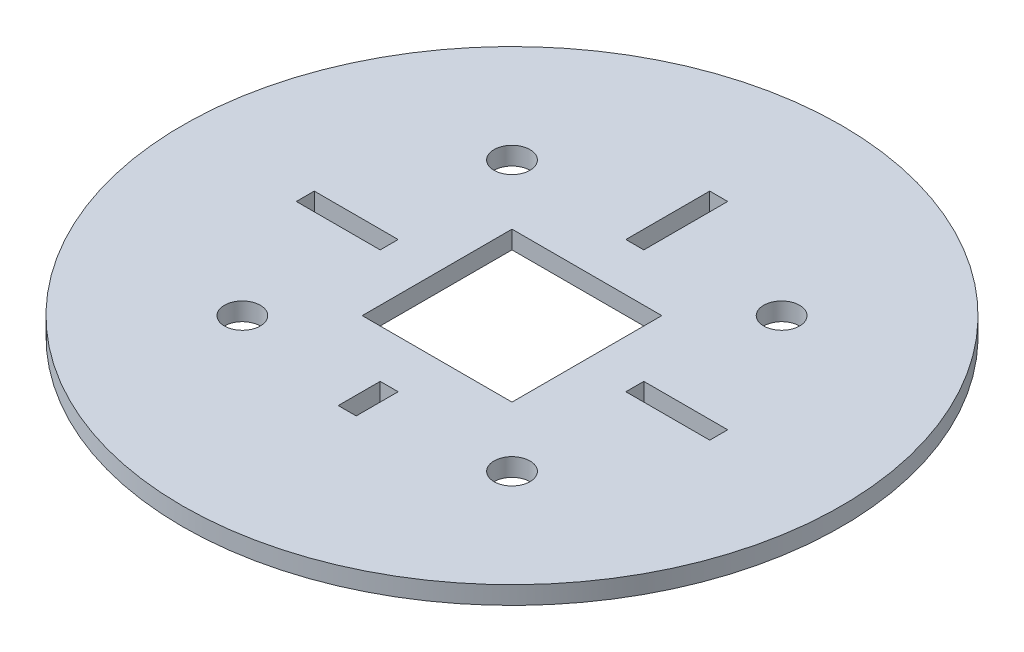
SolidWorks part; units mm, degrees
ref_plane "Front Plane" through (0, 0, 0) normal (0, 0, 1) x (1, 0, 0)
ref_plane "Top Plane" through (0, 0, 0) normal (0, 1, 0) x (1, 0, 0)
ref_plane "Right Plane" through (0, 0, 0) normal (1, 0, 0) x (0, 0, -1)
sketch "Sketch1" plane through (0, 0, 0) normal (0, 1, 0) x (1, 0, 0)
  circle A0 centre (0, 0) radius 55
  dimension "D1" = 110
extrude "Boss-Extrude1" add sketch "Sketch1" along normal blind 3 contours A0
sketch "Sketch2" plane through (0, 3, 0) normal (0, 1, 0) x (1, 0, 0)
  line L0 (0, 0) -> (0, 27.5) construction
  line L1 (12.5, 12.5) -> (-12.5, 12.5)
  line L2 (12.5, 12.5) -> (12.5, -12.5)
  line L3 (12.5, -12.5) -> (-12.5, -12.5)
  line L4 (-12.5, 12.5) -> (-12.5, -12.5)
  line L5 (12.5, 12.5) -> (-12.5, -12.5) construction
  line L6 (12.5, -12.5) -> (-12.5, 12.5) construction
  line L8 (1.5, 34.5) -> (-1.5, 20.5) construction
  line L9 (-1.5, 34.5) -> (1.5, 20.5) construction
  line L10 (-1.5, 20.5) -> (1.5, 20.5)
  line L11 (1.5, 34.5) -> (1.5, 20.5)
  line L12 (-1.5, 34.5) -> (1.5, 34.5)
  line L13 (-34.5, 1.5) -> (-20.5, 1.5)
  line L14 (-34.5, 1.5) -> (-34.5, -1.5)
  line L15 (-34.5, -1.5) -> (-20.5, -1.5)
  line L16 (-20.5, 1.5) -> (-20.5, -1.5)
  line L17 (-34.5, 1.5) -> (-20.5, -1.5) construction
  line L18 (-34.5, -1.5) -> (-20.5, 1.5) construction
  line L19 (-1.5, 34.5) -> (-1.5, 20.5)
  line L20 (20.5, 1.5) -> (34.5, 1.5)
  line L21 (-1.5, -20.5) -> (1.5, -20.5)
  line L22 (-1.5, -20.5) -> (-1.5, -27.5)
  line L23 (-1.5, -27.5) -> (1.5, -27.5)
  line L24 (1.5, -20.5) -> (1.5, -27.5)
  line L25 (-1.5, -20.5) -> (1.5, -27.5) construction
  line L26 (20.5, 1.5) -> (20.5, -1.5)
  line L27 (20.5, -1.5) -> (34.5, -1.5)
  line L28 (34.5, 1.5) -> (34.5, -1.5)
  line L29 (20.5, 1.5) -> (34.5, -1.5) construction
  line L30 (20.5, -1.5) -> (34.5, 1.5) construction
  line L32 (-1.5, -27.5) -> (1.5, -20.5) construction
  circle A0 centre (-22.5, 22.5) radius 3
  circle A1 centre (22.5, 22.5) radius 3
  circle A2 centre (22.5, -22.5) radius 3
  circle A3 centre (-22.5, -22.5) radius 3
  point P8 (27.5, 0)
  point P13 (0, -24)
  point P35 (20.5, 0)
  dimension "D7" = 6
  dimension "D20" = 6
  dimension "D21" = 22.5
  dimension "D1" = 25
  dimension "D2" = 25
  dimension "D3" = 20.5
  dimension "D4" = 1.5
  dimension "D5" = 3
  dimension "D6" = 14
  dimension "D8" = 10
  dimension "D9" = 10
  dimension "D10" = 24
  dimension "D11" = 7
  dimension "D12" = 3
  dimension "D13" = 14
  dimension "D14" = 3
  dimension "D15" = 1.5
  dimension "D16" = 27.5
  dimension "D17" = 20.5
  dimension "D18" = 20.5
  dimension "D19" = 31.8198
extrude "Cut-Extrude1" cut sketch "Sketch2" against normal blind 3
sketch "Sketch4" plane through (0, 3, 0) normal (0, 1, 0) x (1, 0, 0)
  text T0 "HX1" font "Century Gothic" height in points 20
  dimension "D1" = 3.5457
  dimension "D2" = 33.8813
